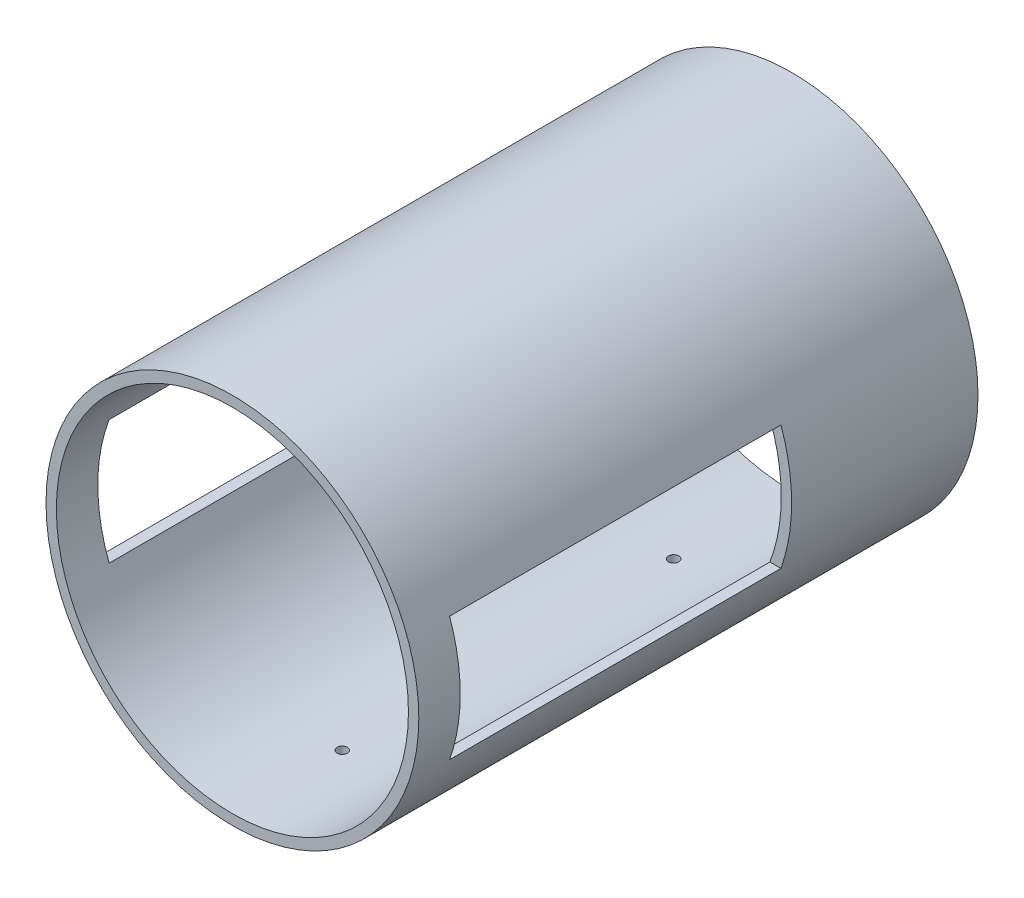
SolidWorks part; units mm, degrees
material "PVC 0.007 Plasticized"
ref_plane "Front Plane" through (0, 0, 0) normal (0, 0, 1) x (1, 0, 0)
ref_plane "Top Plane" through (0, 0, 0) normal (0, 1, 0) x (1, 0, 0)
ref_plane "Right Plane" through (0, 0, 0) normal (1, 0, 0) x (0, 0, -1)
sketch "Sketch1" plane through (0, 0, 0) normal (0, 0, 1) x (1, 0, 0)
  circle A0 centre (0, 0) radius 85
  circle A1 centre (0, 0) radius 90
  dimension "D1" = 170
  dimension "D2" = 180
extrude "Boss-Extrude1" add sketch "Sketch1" along normal blind 270
ref_plane "Plane1" through (10, 0, 0) normal (1, 0, 0) x (0, 0, -1)
sketch "Sketch2" plane through (10, 0, 0) normal (1, 0, 0) x (0, 0, -1)
  line L0 (-270, 0) -> (0, 0) construction
  line L1 (-270, 90) -> (-270, -90) construction
  line L3 (-250, -30) -> (-90, -30)
  line L4 (-250, -30) -> (-250, 30)
  line L5 (-250, 30) -> (-90, 30)
  line L6 (-90, -30) -> (-90, 30)
  point P5 (-135, 0)
  point P10 (0, 0)
  point P11 (0, 0)
  dimension "D1" = 160
  dimension "D2" = 60
extrude "Cut-Extrude1" cut sketch "Sketch2" against normal through all both and the other way through all
ref_plane "Plane2" through (0, 10, 0) normal (0, 1, 0) x (1, 0, 0)
sketch "Sketch3" plane through (0, 10, 0) normal (0, 1, 0) x (1, 0, 0)
  line L0 (0, 0) -> (0, -270) construction
  line L1 (-90, -270) -> (90, -270) construction
  line L2 (-11.7603, -136.9355) -> (13.392, -136.9355) construction
  circle A2 centre (0, -216.9355) radius 2.5
  circle A3 centre (0, -56.9355) radius 2.5
  point P7 (0, 0)
  dimension "D2" = 160
  dimension "D1" = 5
extrude "Cut-Extrude2" cut sketch "Sketch3" against normal blind 200
